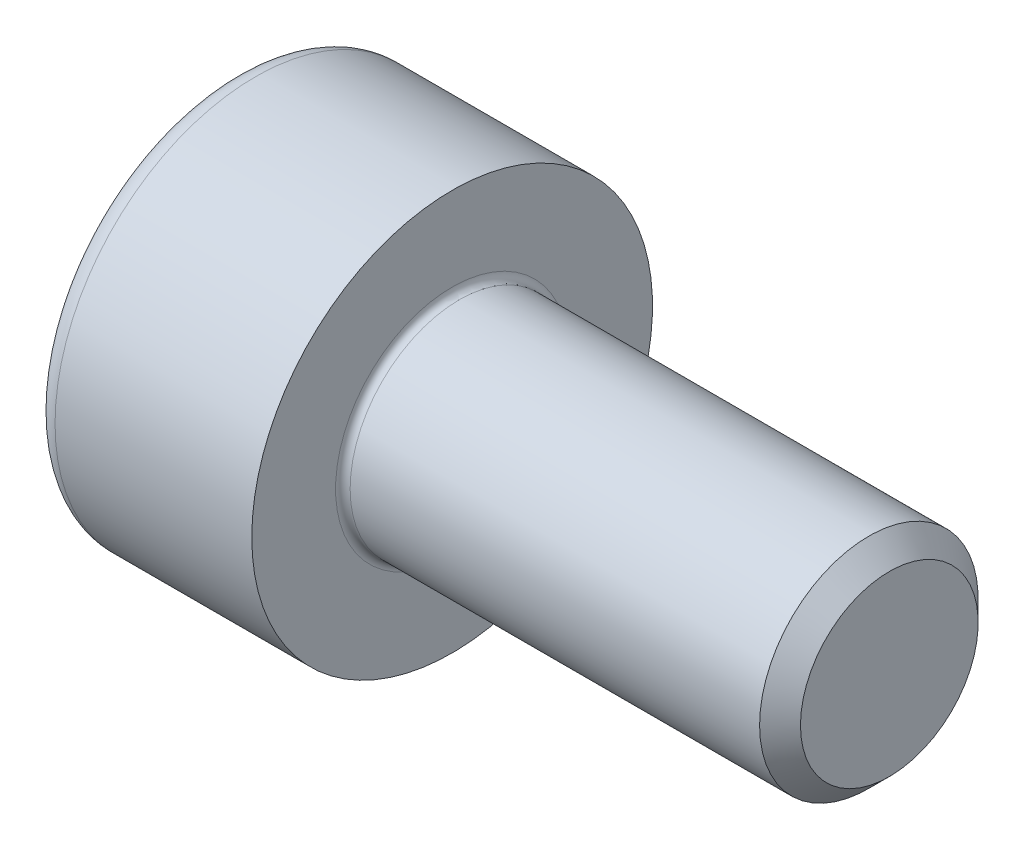
SolidWorks part; units mm, degrees
material "Alloy Steel"
ref_plane "Plane1" through (0, 0, 0) normal (0, 0, 1) x (1, 0, 0)
ref_plane "Plane2" through (0, 0, 0) normal (0, 1, 0) x (1, 0, 0)
ref_plane "Plane3" through (0, 0, 0) normal (1, 0, 0) x (0, 0, -1)
sketch "BodySke" plane through (0, 0, 0) normal (0, 0, 1) x (1, 0, 0)
  line L0 (0, 0) -> (0, 2.75)
  line L1 (0, 2.75) -> (3, 2.75)
  line L2 (3, 2.75) -> (3, 1.5)
  line L3 (3, 1.5) -> (8.7195, 1.5)
  line L4 (9, 1.2195) -> (9, 0)
  line L5 (9, 0) -> (0, 0)
  line L6 (-31.75, 0) -> (127, 0) construction
  line L8 (9, 1.2195) -> (8.7195, 1.5)
  line L10 (9, -1.2195) -> (8.7195, -1.5) construction
  line L11 (3.5, 9.525) -> (3.5, 3.175) construction
  line L12 (-1, 9.525) -> (-1, 3.175) construction
  line L13 (-51, 9.525) -> (-51, 3.175) construction
  dimension "Diameter" = 3
  dimension "Head_ht" = 3
  dimension "Length" = 6
  dimension "Body_ch_ang" = 45
  dimension "Head_dia" = 5.5
  dimension "Minor_dia" = 2.439
  dimension "Advance" = 0.5
  dimension "Thread_nom" = 10
  dimension "Thread_length" = 60
revolve "Base-Revolve" add sketch "BodySke"
cosmetic thread "ThreadCosmetic" [suppressed]
fillet "Fillet1" radius 0.1 1 edges at (3, 0, 1.5)
fillet "Fillet2" radius 0.3 1 edges at (0, 0, 2.75)
sketch "Sketch2" plane through (0, 0, 0) normal (0, 0, 1) x (1, 0, 0)
  line L0 (0, 1.26) -> (1.3, 1.26)
  line L1 (1.3, 1.26) -> (2.0275, 0)
  line L2 (-31.75, 0) -> (127, 0) construction
  line L3 (2.0275, 0) -> (0, 0)
  line L4 (0, 0) -> (0, 1.26)
  line L6 (0, 0) -> (47.625, 0) construction
  dimension "D1" = 1.26
  dimension "D2" = 60
  dimension "Depth" = 1.3
revolve "Hex-PreBroach" cut sketch "Sketch2" angle 360 about L6
sketch "Sketch3" plane through (0, 0, 0) normal (-1, 0, 0) x (0, 0.5, 0.866)
  line L0 (0.7275, 1.26) -> (-0.7275, 1.26)
  line L1 (-0.7275, 1.26) -> (-1.4549, 0)
  line L2 (0.7275, 1.26) -> (1.4549, 0)
  line L3 (0.7275, -1.26) -> (1.4549, 0)
  line L4 (0.7275, -1.26) -> (-0.7275, -1.26)
  line L5 (-0.7275, -1.26) -> (-1.4549, 0)
  dimension "D1" = 1.26
  dimension "D2" = 1.26
  dimension "Hex_size" = 2.52
extrude "Hex" cut sketch "Sketch3" against normal blind 1.3
sketch "ThdSchSke" plane through (0, 0, 0) normal (0, 0, 1) x (1, 0, 0)
  line L0 (4.5, -1.2195) -> (4.3036, -1.5)
  line L1 (4.5, -1.2195) -> (4.6964, -1.5)
  line L2 (4.6964, -1.5) -> (4.6964, -1.875)
  line L3 (-3.175, 0) -> (5.1513, 0) construction
  line L4 (0, 2.45) -> (0, -2.45) construction
  line L5 (4.6964, -1.875) -> (4.3036, -1.875)
  line L6 (4.3036, -1.875) -> (4.3036, -1.5)
  dimension "Thread_minor" = 2.439
  dimension "Diameter" = 3
  dimension "Start" = 4.5
  dimension "SideAngle" = 55
  dimension "VeeAngle" = 70
  dimension "Overcut" = 3.75
revolve "ThreadSchematic" [suppressed] cut sketch "ThdSchSke" angle 360 about L3
pattern_linear "ThdSchPat" [suppressed]
equation "\"D2@Sketch3\" = \"Hex_size@Sketch3\" / 2"
equation "\"D1@Sketch3\" = \"Hex_size@Sketch3\" / 2"
equation "\"D1@Sketch2\" = \"Hex_size@Sketch3\" / 2"
equation "\"Thread_minor@ThreadCosmetic\"  =  \"Minor_dia@BodySke\""
equation "\"Depth@Sketch2\" =  \"Key_eng@Hex\""
equation "\"Thread_length@ThreadCosmetic\" = ((sgn( (\"Length@BodySke\" - \"Advance@BodySke\" * 3.0) - \"Thread_nom@BodySke\" )-1)*( (\"Length@BodySke\" - \"Advance@BodySke\" * 3.0) - \"Thread_nom@BodySke\" ))/-2+ \"Thread_nom@BodySke\""
equation "\"Thread_minor@ThdSchSke\" = \"Minor_dia@BodySke\""
equation "\"Diameter@ThdSchSke\" = \"Diameter@BodySke\""
equation "\"Overcut@ThdSchSke\" = \"Diameter@BodySke\" * 1.25"
equation "\"Start@ThdSchSke\" = \"Head_ht@BodySke\" + \"Length@BodySke\" - \"Thread_length@ThreadCosmetic\"  '---Non-countersunk---"
equation "\"Num_threads@ThdSchPat\" = int( \"Thread_length@ThreadCosmetic\" / \"Advance@BodySke\" + 0.999 )  + 1"
equation "\"Advance@ThdSchPat\" = \"Thread_length@ThreadCosmetic\" /  (\"Num_threads@ThdSchPat\" - 1) 'relax it"
equation "\"Num_threads@ThdSchPat\" = \"Num_threads@ThdSchPat\" - sgn( \"Num_threads@ThdSchPat\" - 1) '---chamfered tips only---"
